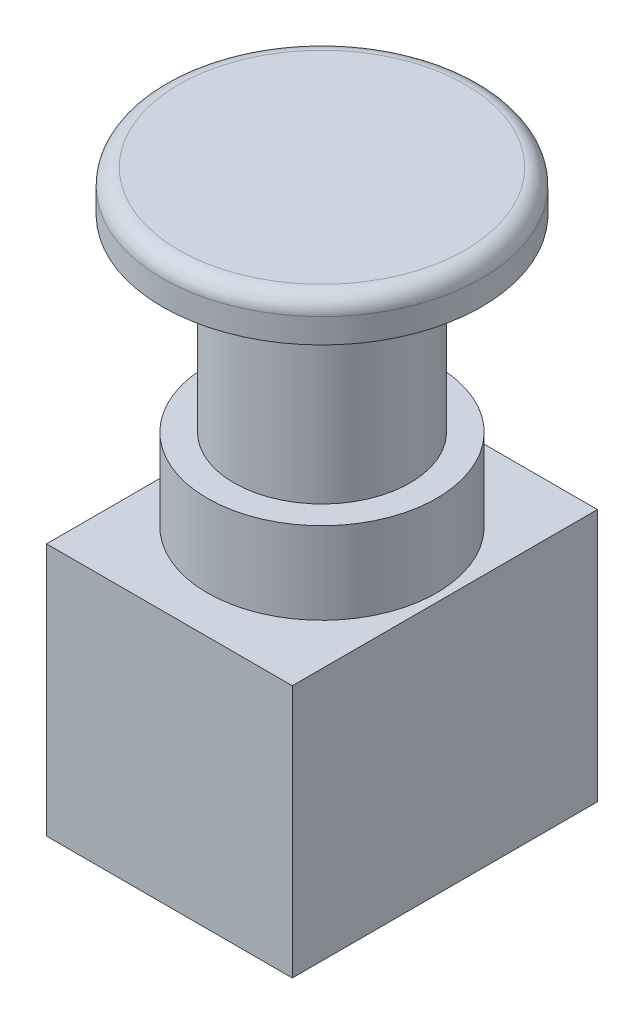
SolidWorks part; units mm, degrees
ref_plane "Front Plane" through (0, 0, 0) normal (0, 0, 1) x (1, 0, 0)
ref_plane "Top Plane" through (0, 0, 0) normal (0, 1, 0) x (1, 0, 0)
ref_plane "Right Plane" through (0, 0, 0) normal (1, 0, 0) x (0, 0, -1)
sketch "Sketch1" plane through (0, 0, 0) normal (0, 1, 0) x (1, 0, 0)
  line L1 (-15, -18.625) -> (15, -18.625)
  line L2 (-15, -18.625) -> (-15, 18.625)
  line L3 (-15, 18.625) -> (15, 18.625)
  line L4 (15, -18.625) -> (15, 18.625)
  line L5 (-15, -18.625) -> (15, 18.625) construction
  line L6 (-15, 18.625) -> (15, -18.625) construction
  point P0 (0, 0)
  dimension "D1" = 30
  dimension "D2" = 37.25
extrude "Boss-Extrude1" add sketch "Sketch1" along normal blind 30.9
sketch "Sketch2" plane through (0, 30.9, 0) normal (0, 1, 0) x (1, 0, 0)
  circle A0 centre (0, 0) radius 14
  dimension "D1" = 28
extrude "Boss-Extrude2" add sketch "Sketch2" along normal blind 10
sketch "Sketch3" plane through (0, 40.9, 0) normal (0, 1, 0) x (1, 0, 0)
  circle A0 centre (0, 0) radius 10.75
  dimension "D1" = 21.5
extrude "Boss-Extrude3" add sketch "Sketch3" along normal blind 23
sketch "Sketch4" plane through (0, 63.9, 0) normal (0, 1, 0) x (1, 0, 0)
  circle A0 centre (0, 0) radius 19.5
  dimension "D1" = 39
extrude "Boss-Extrude4" add sketch "Sketch4" along normal blind 5 separate body
fillet "Fillet1" radius 2 1 edges at (0, 68.9, 19.5)
